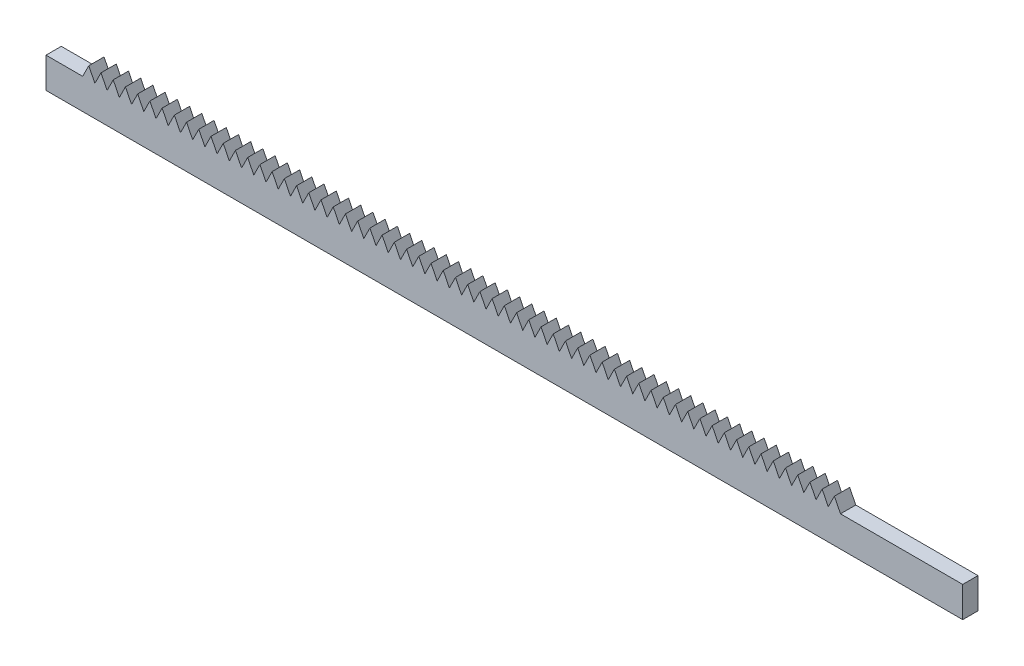
SolidWorks part; units mm, degrees
ref_plane "Front Plane" through (0, 0, 0) normal (0, 0, 1) x (1, 0, 0)
ref_plane "Top Plane" through (0, 0, 0) normal (0, 1, 0) x (1, 0, 0)
ref_plane "Right Plane" through (0, 0, 0) normal (1, 0, 0) x (0, 0, -1)
sketch "Sketch1" plane through (0, 0, 0) normal (0, 0, 1) x (1, 0, 0)
  line L1 (0, 0) -> (190.5, 0)
  line L2 (0, 0) -> (0, 6.35)
  line L3 (0, 6.35) -> (190.5, 6.35)
  line L4 (190.5, 0) -> (190.5, 6.35)
  dimension "D1" = 190.5
  dimension "D2" = 6.35
extrude "Boss-Extrude1" add sketch "Sketch1" along normal blind 3.175
sketch "Sketch2" plane through (0, 0, 3.175) normal (0, 0, 1) x (1, 0, 0)
  line L0 (165.1, 6.35) -> (163.83, 8.89)
  line L1 (190.5, 6.35) -> (0, 6.35) construction
  line L2 (163.83, 8.89) -> (162.56, 6.35)
  line L3 (162.56, 6.35) -> (165.1, 6.35)
  line L4 (190.5, 0) -> (190.5, 6.35) construction
  point P7 (0, 0)
  dimension "D1" = 2.54
  dimension "D2" = 25.4
  dimension "D3" = 2.54
extrude "Boss-Extrude2" add sketch "Sketch2" against normal up to surface (3.175 mm away) up to face at (95.25, 3.175, 0)
ref_plane "Plane2" through (6.35, 0, 0) normal (1, 0, 0) x (0, 0, -1)
pattern_linear "LPattern1" count 62 spacing 2.54 along (-1, 0, 0) of "Boss-Extrude2"
